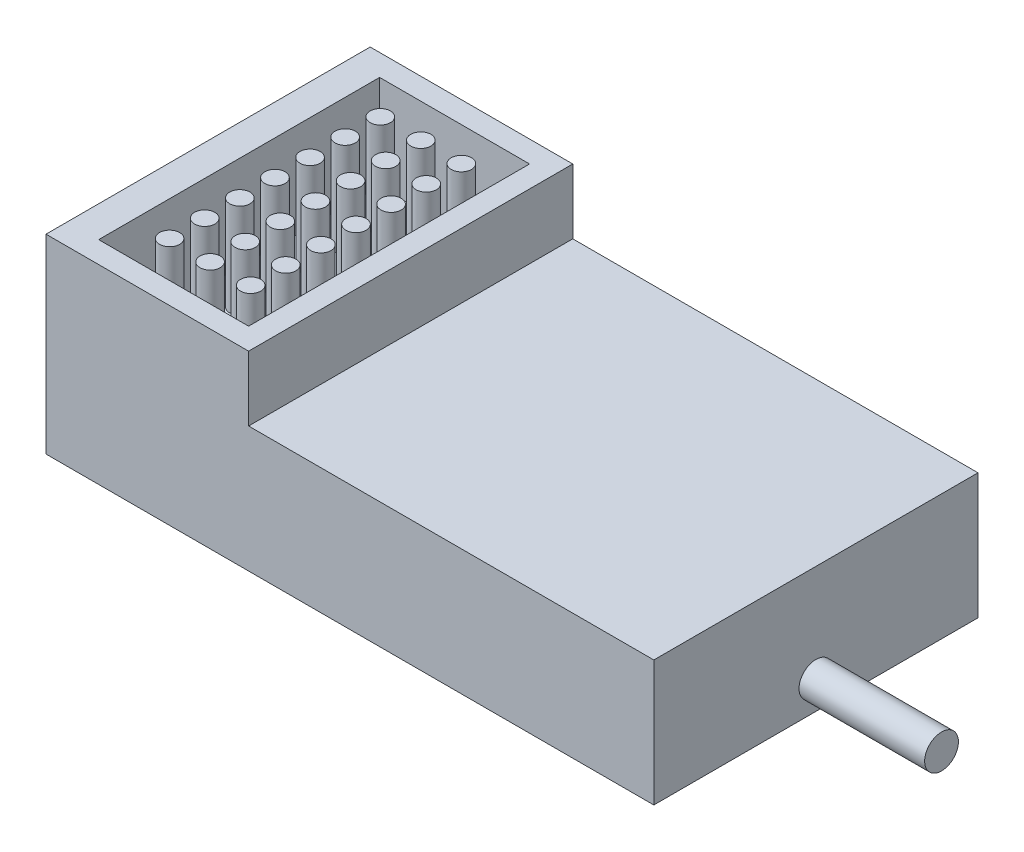
SolidWorks part; units mm, degrees
ref_plane "Front Plane" through (0, 0, 0) normal (0, 0, 1) x (1, 0, 0)
ref_plane "Top Plane" through (0, 0, 0) normal (0, 1, 0) x (1, 0, 0)
ref_plane "Right Plane" through (0, 0, 0) normal (1, 0, 0) x (0, 0, -1)
sketch "Sketch1" plane through (0, 0, 0) normal (0, 1, 0) x (1, 0, 0)
  line L1 (0, 0) -> (45, 0)
  line L2 (0, 0) -> (0, 24)
  line L3 (0, 24) -> (45, 24)
  line L4 (45, 0) -> (45, 24)
  dimension "D1" = 45
  dimension "D2" = 24
extrude "Boss-Extrude1" add sketch "Sketch1" along normal blind 9.3
sketch "Sketch2" plane through (45, 0, 0) normal (1, 0, 0) x (0, 0, -1)
  line L0 (0, 0) -> (24, 0) construction
  circle A0 centre (12, 2.0834) radius 1.25
  point P4 (12, 0)
  dimension "D1" = 2.5
  dimension "D2" = 2.0834
extrude "Boss-Extrude2" add sketch "Sketch2" along normal blind 9.3
sketch "Sketch3" plane through (0, 9.3, 0) normal (0, 1, 0) x (1, 0, 0)
  line L0 (0, 0) -> (45, 0) construction
  line L1 (0, 24) -> (15, 24)
  line L2 (0, 24) -> (0, 0)
  line L3 (0, 0) -> (15, 0)
  line L4 (15, 24) -> (15, 0)
  dimension "D1" = 15
extrude "Boss-Extrude3" add sketch "Sketch3" along normal blind 4.8
sketch "Sketch4" plane through (0, 14.1, 0) normal (0, 1, 0) x (1, 0, 0)
  line L0 (15, 0) -> (15, 24) construction
  line L1 (2.3, 22.4) -> (13.4, 22.4)
  line L2 (2.3, 22.4) -> (2.3, 1.6)
  line L3 (2.3, 1.6) -> (13.4, 1.6)
  line L4 (13.4, 22.4) -> (13.4, 1.6)
  line L5 (13.4, 1.6) -> (13.4, 0) construction
  line L6 (0, 0) -> (15, 0) construction
  line L7 (13.4, 1.6) -> (15, 1.6) construction
  line L8 (0, 24) -> (0, 0) construction
  line L9 (4.85, 19.9) -> (7.85, 19.9) construction
  line L10 (7.85, 19.9) -> (10.85, 19.9) construction
  line L11 (4.85, 19.9) -> (2.3, 19.9) construction
  line L12 (10.85, 19.9) -> (13.4, 19.9) construction
  circle A0 centre (4.85, 19.9) radius 0.75
  circle A1 centre (7.85, 19.9) radius 0.75
  circle A2 centre (10.85, 19.9) radius 0.75
  circle A3 centre (4.85, 17.3) radius 0.75
  circle A4 centre (7.85, 17.3) radius 0.75
  circle A5 centre (10.85, 17.3) radius 0.75
  circle A6 centre (4.85, 14.7) radius 0.75
  circle A7 centre (7.85, 14.7) radius 0.75
  circle A8 centre (10.85, 14.7) radius 0.75
  circle A9 centre (4.85, 12.1) radius 0.75
  circle A10 centre (7.85, 12.1) radius 0.75
  circle A11 centre (10.85, 12.1) radius 0.75
  circle A12 centre (4.85, 9.5) radius 0.75
  circle A13 centre (7.85, 9.5) radius 0.75
  circle A14 centre (10.85, 9.5) radius 0.75
  circle A15 centre (4.85, 6.9) radius 0.75
  circle A16 centre (7.85, 6.9) radius 0.75
  circle A17 centre (10.85, 6.9) radius 0.75
  circle A18 centre (4.85, 4.3) radius 0.75
  circle A19 centre (7.85, 4.3) radius 0.75
  circle A20 centre (10.85, 4.3) radius 0.75
  point P4 (13.4, 12)
  point P7 (15, 12)
  dimension "D3" = 1.5
  dimension "D1" = 1.6
  dimension "D2" = 2.3
  dimension "D4" = 3
  dimension "D5" = 2.5
  dimension "D6" = 7
extrude "Cut-Extrude1" cut sketch "Sketch4" against normal blind 7
